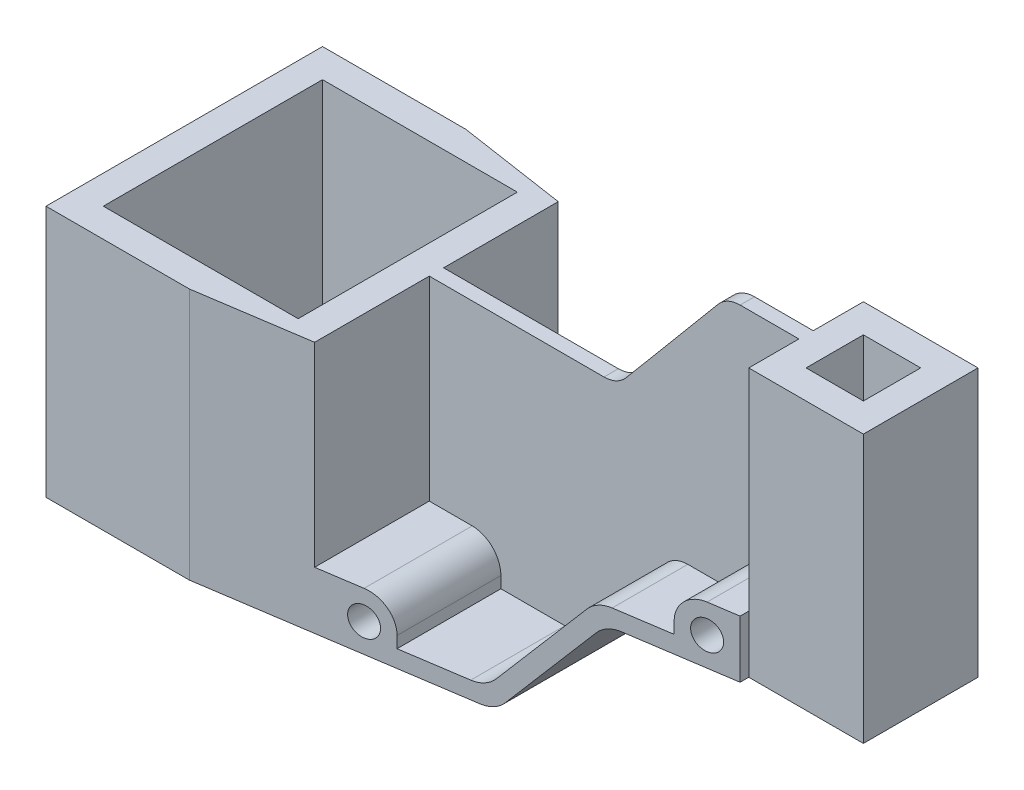
SolidWorks part; units mm, degrees
material "1060 Alloy"
ref_plane "Front Plane" through (0, 0, 0) normal (0, 0, 1) x (1, 0, 0)
ref_plane "Top Plane" through (0, 0, 0) normal (0, 1, 0) x (1, 0, 0)
ref_plane "Right Plane" through (0, 0, 0) normal (1, 0, 0) x (0, 0, -1)
sketch "Sketch1" plane through (0, 0, 0) normal (0, 1, 0) x (1, 0, 0)
  line L1 (0, 0) -> (-257, 0)
  line L2 (0, 0) -> (0, -96.5)
  line L3 (0, -96.5) -> (-257, -96.5)
  line L4 (-257, 0) -> (-257, -96.5)
  dimension "D1" = 257
  dimension "D2" = 96.5
extrude "Boss-Extrude1" add sketch "Sketch1" along normal blind 133.5
sketch "Sketch2" plane through (0, 133.5, 0) normal (0, 1, 0) x (1, 0, 0)
  line L0 (-257, -96.5) -> (0, -96.5) construction
  line L1 (-257, 0) -> (-117, 0)
  line L2 (-257, 0) -> (-257, -96.5)
  line L3 (-257, -96.5) -> (-117, -96.5)
  line L4 (-117, 0) -> (-117, -96.5)
  dimension "D1" = 140
extrude "Cut-Extrude1" cut sketch "Sketch2" against normal blind 45.5
sketch "Sketch3" plane through (0, 88, 0) normal (0, 1, 0) x (1, 0, 0)
  line L0 (-257, -48.25) -> (-89.9232, -48.25) construction
  line L1 (-257, 0) -> (-257, -96.5) construction
  line L2 (-117, 0) -> (-117, -45.75)
  line L3 (-117, -96.5) -> (-169, -96.5)
  line L4 (-117, -96.5) -> (-117, -50.75)
  line L5 (-117, -50.75) -> (-169, -50.75)
  line L6 (-169, -96.5) -> (-169, -50.75)
  line L7 (-117, 0) -> (-169, 0)
  line L8 (-169, 0) -> (-169, -45.75)
  line L9 (-117, -45.75) -> (-169, -45.75)
  dimension "D1" = 2.5
  dimension "D2" = 52
extrude "Cut-Extrude2" cut sketch "Sketch3" against normal blind 68
sketch "Sketch4" plane through (0, 88, 0) normal (0, 1, 0) x (1, 0, 0)
  line L0 (-257, 0) -> (-257, -96.5) construction
  line L1 (-247, -10) -> (-179, -10)
  line L2 (-247, -10) -> (-247, -86.5)
  line L3 (-247, -86.5) -> (-179, -86.5)
  line L4 (-179, -10) -> (-179, -86.5)
  line L5 (-169, 0) -> (-257, 0) construction
  line L6 (-169, 0) -> (-169, -45.75) construction
  line L7 (-257, -96.5) -> (-169, -96.5) construction
  dimension "D1" = 10
  dimension "D2" = 10
  dimension "D3" = 10
  dimension "D4" = 10
extrude "Cut-Extrude3" cut sketch "Sketch4" against normal through all
sketch "Sketch5" plane through (0, 0, 96.5) normal (0, 0, 1) x (1, 0, 0)
  line L0 (-169, 20) -> (-154, 20)
  line L1 (-169, 20) -> (-117, 20) construction
  line L2 (-169, 20) -> (-169, 88)
  line L3 (-257, 88) -> (-257, 0) construction
  line L4 (-257, 0) -> (0, 0) construction
  line L5 (-144, 10) -> (-144, 6)
  line L6 (-144, 6) -> (-117, 6)
  line L7 (-169, 88) -> (-117, 88)
  line L8 (-117, 88) -> (-117, 6)
  circle A0 centre (-154, 10) radius 5
  arc A1 (-154, 20) -> (-144, 10) centre (-154, 10) cw
  point P11 (-128.5, 0)
  dimension "D4" = 10
  dimension "D1" = 103
  dimension "D3" = 140
extrude "Cut-Extrude4" cut sketch "Sketch5" against normal blind 45.75
sketch "Sketch6" plane through (0, 0, 0) normal (0, 0, -1) x (-1, 0, 0)
  line L0 (144, 6) -> (117, 6)
  line L1 (117, 6) -> (117, 88)
  line L2 (117, 88) -> (169, 88)
  line L3 (169, 88) -> (169, 20)
  line L4 (169, 20) -> (154, 20)
  line L5 (144, 10) -> (144, 6)
  arc A0 (154, 20) -> (144, 10) centre (154, 10) ccw
  circle A1 centre (154, 10) radius 5
extrude "Cut-Extrude5" cut sketch "Sketch6" against normal blind 45.75
sketch "Sketch7" plane through (0, 0, 0) normal (0, 0, -1) x (-1, 0, 0)
  circle A0 centre (154, 10) radius 5 construction
  circle A1 centre (154, 10) radius 5
extrude "Cut-Extrude6" cut sketch "Sketch7" against normal through all
sketch "Sketch8" plane through (0, 0, 96.5) normal (0, 0, 1) x (1, 0, 0)
  line L0 (-117, 6) -> (-68.4171, 63.8988)
  line L1 (-144, 6) -> (-117, 6) construction
  line L2 (-80.6382, 40) -> (-114.2022, 0)
  line L3 (-257, 0) -> (0, 0) construction
  line L4 (-80.6382, 40) -> (0, 40)
  line L5 (0, 133.5) -> (0, 0) construction
  line L6 (0, 40) -> (0, 0)
  line L7 (0, 0) -> (-114.2022, 0)
  line M13 (-257, 0) -> (0, 0)
  line M14 (0, 0) -> (0, 133.5)
  dimension "D1" = 130
  dimension "D2" = 6
  dimension "D3" = 40
extrude "Cut-Extrude7" cut sketch "Sketch8" against normal through all contours L4 L2 M13 M14
sketch "Sketch9" plane through (0, 0, 96.5) normal (0, 0, 1) x (1, 0, 0)
  line L0 (-65.1683, 133.5) -> (-103.3473, 88)
  line L1 (-117, 133.5) -> (0, 133.5) construction
  line L2 (-80.6382, 40) -> (-114.2022, 0) construction
  line L3 (-65.1683, 133.5) -> (-117, 133.5)
  line L4 (-117, 133.5) -> (-117, 88)
  line L5 (-117, 88) -> (-103.3473, 88)
  dimension "D1" = 48.25
extrude "Cut-Extrude8" cut sketch "Sketch9" against normal through all
sketch "Sketch10" plane through (0, 0, 96.5) normal (0, 0, 1) x (1, 0, 0)
  line L0 (-83.436, 46) -> (-60, 46)
  line L1 (-117, 6) -> (-68.4171, 63.8988) construction
  line L2 (-50, 60) -> (-40, 60)
  line L3 (-40, 60) -> (-40, 133.5)
  line L4 (-65.1683, 133.5) -> (0, 133.5) construction
  line L5 (-80.6382, 40) -> (0, 40) construction
  line L6 (0, 133.5) -> (0, 40) construction
  line L7 (-60, 50) -> (-60, 46)
  line L8 (-40, 133.5) -> (-65.1683, 133.5)
  line L9 (-65.1683, 133.5) -> (-103.3473, 88)
  line L10 (-103.3473, 88) -> (-117, 88)
  line L11 (-117, 88) -> (-117, 6)
  line L12 (-117, 6) -> (-83.436, 46)
  circle A0 centre (-50, 50) radius 5
  arc A1 (-50, 60) -> (-60, 50) centre (-50, 50) ccw
  dimension "D5" = 10
  dimension "D6" = 10
  dimension "D1" = 6
  dimension "D2" = 20
  dimension "D3" = 40
  dimension "D4" = 50
extrude "Cut-Extrude9" cut sketch "Sketch10" against normal blind 45.75
sketch "Sketch11" plane through (0, 0, 0) normal (0, 0, -1) x (-1, 0, 0)
  line L0 (65.1683, 133.5) -> (40, 133.5)
  line L1 (40, 133.5) -> (40, 60)
  line L2 (40, 60) -> (50, 60)
  line L3 (60, 50) -> (60, 46)
  line L4 (60, 46) -> (83.436, 46)
  line L5 (83.436, 46) -> (117, 6)
  line L6 (117, 6) -> (117, 88)
  line L7 (117, 88) -> (103.3473, 88)
  line L8 (103.3473, 88) -> (65.1683, 133.5)
  arc A0 (50, 60) -> (60, 50) centre (50, 50) cw
extrude "Cut-Extrude10" cut sketch "Sketch11" against normal blind 45.75
sketch "Sketch12" plane through (0, 0, 0) normal (0, 0, -1) x (-1, 0, 0)
  circle A0 centre (50, 50) radius 5
extrude "Cut-Extrude11" cut sketch "Sketch12" against normal through all
sketch "Sketch13" plane through (0, 133.5, 0) normal (0, 1, 0) x (1, 0, 0)
  line L0 (-40, -68.25) -> (0, -68.25)
  line L1 (-40, -50.75) -> (-40, -96.5) construction
  line L2 (0, -96.5) -> (0, 0) construction
  line L3 (-40, -96.5) -> (0, -96.5) construction
  line L4 (-40, -68.25) -> (-40, -96.5)
  line L5 (-40, -96.5) -> (0, -96.5)
  line L6 (0, -96.5) -> (0, -68.25)
  line L7 (-40, -28.25) -> (0, -28.25)
  line L8 (-40, -45.75) -> (-40, 0) construction
  line L9 (0, -28.25) -> (0, 0)
  line L10 (0, 0) -> (-40, 0)
  line L11 (-40, 0) -> (-40, -28.25)
  dimension "D1" = 28.25
  dimension "D2" = 28.25
extrude "Cut-Extrude12" cut sketch "Sketch13" against normal through all
sketch "Sketch14" plane through (0, 133.5, 0) normal (0, 1, 0) x (1, 0, 0)
  line L0 (-40, -28.25) -> (0, -28.25) construction
  line L1 (-30, -38.25) -> (-10, -38.25)
  line L2 (-30, -38.25) -> (-30, -58.25)
  line L3 (-30, -58.25) -> (-10, -58.25)
  line L4 (-10, -38.25) -> (-10, -58.25)
  line L5 (0, -68.25) -> (0, -28.25) construction
  line L6 (-40, -50.75) -> (-40, -68.25) construction
  line L7 (0, -68.25) -> (-40, -68.25) construction
  dimension "D1" = 10
  dimension "D2" = 10
  dimension "D3" = 10
  dimension "D4" = 10
extrude "Cut-Extrude13" cut sketch "Sketch14" against normal through all
sketch "Sketch15" plane through (0, 88, 0) normal (0, 1, 0) x (1, 0, 0)
  line L0 (-213, 0) -> (-213, -96.5) construction
  line L1 (-169, 0) -> (-257, 0) construction
  line L2 (-257, -96.5) -> (-169, -96.5) construction
  line L3 (-207, 0) -> (-207, -96.5) construction
  line L4 (-20, -28.25) -> (-20, -68.25) construction
  line L5 (-40, -28.25) -> (0, -28.25) construction
  line L6 (0, -68.25) -> (-40, -68.25) construction
  line L7 (-207, 0) -> (-20, -28.25)
  line L8 (-20, -28.25) -> (-20, 0)
  line L9 (-20, 0) -> (-207, 0)
  line L10 (-207, -96.5) -> (-20, -68.25)
  line L11 (-20, -68.25) -> (-20, -96.5)
  line L12 (-20, -96.5) -> (-207, -96.5)
  dimension "D1" = 6
extrude "Cut-Extrude14" cut sketch "Sketch15" against normal through all
fillet "Fillet1" radius 10 7 edges at (-114.2022, 0, 48.25) (-117, 6, 29.6731) (-117, 6, 66.8269) (-83.436, 46, 64.2916) (-83.436, 46, 32.2084) (-65.1683, 133.5, 48.25) (-103.3473, 88, 48.25)
fillet "Fillet2" radius 10 1 edges at (-80.6382, 40, 48.25)
